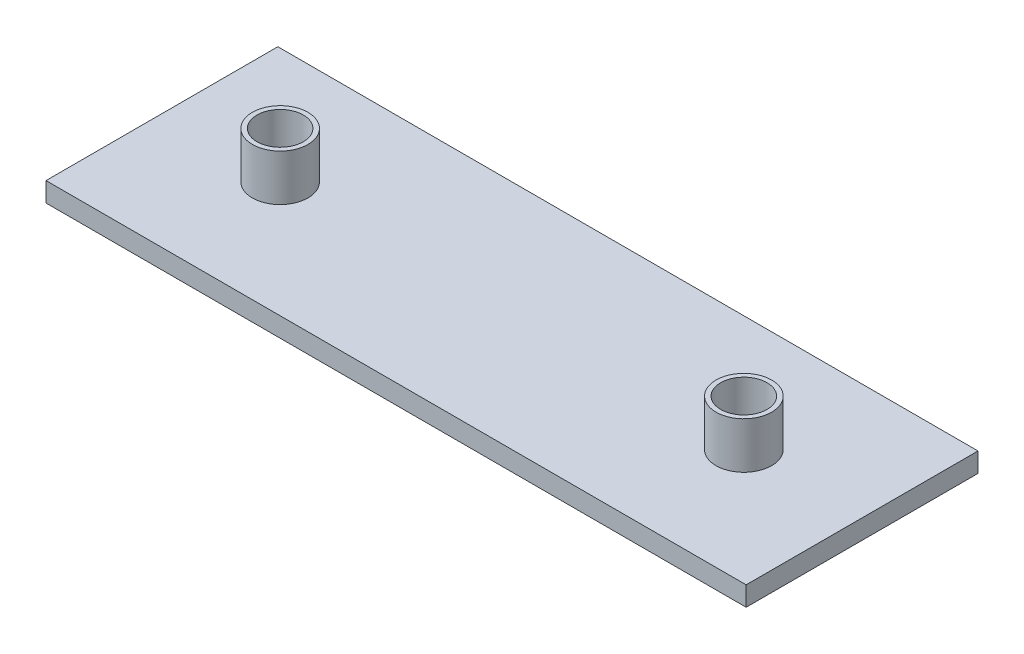
SolidWorks part; units mm, degrees
ref_plane "Front Plane" through (0, 0, 0) normal (0, 0, 1) x (1, 0, 0)
ref_plane "Top Plane" through (0, 0, 0) normal (0, 1, 0) x (1, 0, 0)
ref_plane "Right Plane" through (0, 0, 0) normal (1, 0, 0) x (0, 0, -1)
sketch "Sketch1" plane through (0, 0, 0) normal (0, 1, 0) x (1, 0, 0)
  line L1 (-46.8464, 20.5835) -> (28.6536, 20.5835)
  line L2 (-46.8464, 20.5835) -> (-46.8464, -4.4165)
  line L3 (-46.8464, -4.4165) -> (28.6536, -4.4165)
  line L4 (28.6536, 20.5835) -> (28.6536, -4.4165)
  dimension "D1" = 75.5
  dimension "D2" = 25
extrude "Boss-Extrude1" add sketch "Sketch1" along normal blind 2.1
sketch "Sketch2" plane through (0, 0, 4.4165) normal (0, 0, 1) x (1, 0, 0)
  line L0 (-46.8464, 2.1) -> (-46.8464, 0) construction
  line L1 (28.6536, 2.1) -> (28.6536, 0) construction
  line L2 (28.6536, 1.05) -> (-46.8464, 1.05) construction
  point P0 (-46.8464, 1.05)
  point P1 (28.6536, 1.05)
ref_plane "Plane1" through (0, 1.05, 0) normal (0, -1, 0) x (-1, 0, 0)
sketch "Sketch3" plane through (0, 1.05, 0) normal (0, -1, 0) x (-1, 0, 0)
  line L0 (46.8464, 8.0835) -> (-28.6536, 8.0835) construction
  line L1 (46.8464, 20.5835) -> (46.8464, -4.4165) construction
  line L2 (-28.6536, -4.4165) -> (-28.6536, 20.5835) construction
  line L3 (34.0964, 8.0835) -> (-15.9036, 8.0835) construction
  line L4 (34.0964, 5.5835) -> (-15.9036, 5.5835)
  line L5 (34.0964, 10.5835) -> (-15.9036, 10.5835)
  line L6 (9.0964, -4.4165) -> (9.0964, 37.2239) construction
  line L7 (-28.6536, -4.4165) -> (46.8464, -4.4165) construction
  arc A0 (34.0964, 5.5835) -> (34.0964, 10.5835) centre (34.0964, 8.0835) ccw
  arc A1 (-15.9036, 10.5835) -> (-15.9036, 5.5835) centre (-15.9036, 8.0835) ccw
  point P8 (9.0964, 8.0835)
  dimension "D1" = 5
  dimension "D2" = 50
  dimension "D3" = 0
extrude "Cut-Extrude1" cut sketch "Sketch3" against normal blind 0.2 and the other way blind 0.2
sketch "Sketch4" plane through (0, 2.1, 0) normal (0, 1, 0) x (1, 0, 0)
  circle A0 centre (-34.0964, 8.0835) radius 3
  circle A1 centre (15.9036, 8.0835) radius 3
  circle A2 centre (15.9036, 8.0835) radius 2.5
  circle A3 centre (-34.0964, 8.0835) radius 2.5
  dimension "D1" = 6
extrude "Boss-Extrude2" add sketch "Sketch4" along normal blind 5
sketch "Sketch5" plane through (0, 1.25, 0) normal (0, -1, 0) x (1, 0, 0)
  circle A0 centre (-34.0964, -8.0835) radius 2.5
  circle A1 centre (15.9036, -8.0835) radius 2.5
extrude "Cut-Extrude5" cut sketch "Sketch5" against normal blind 0.5
